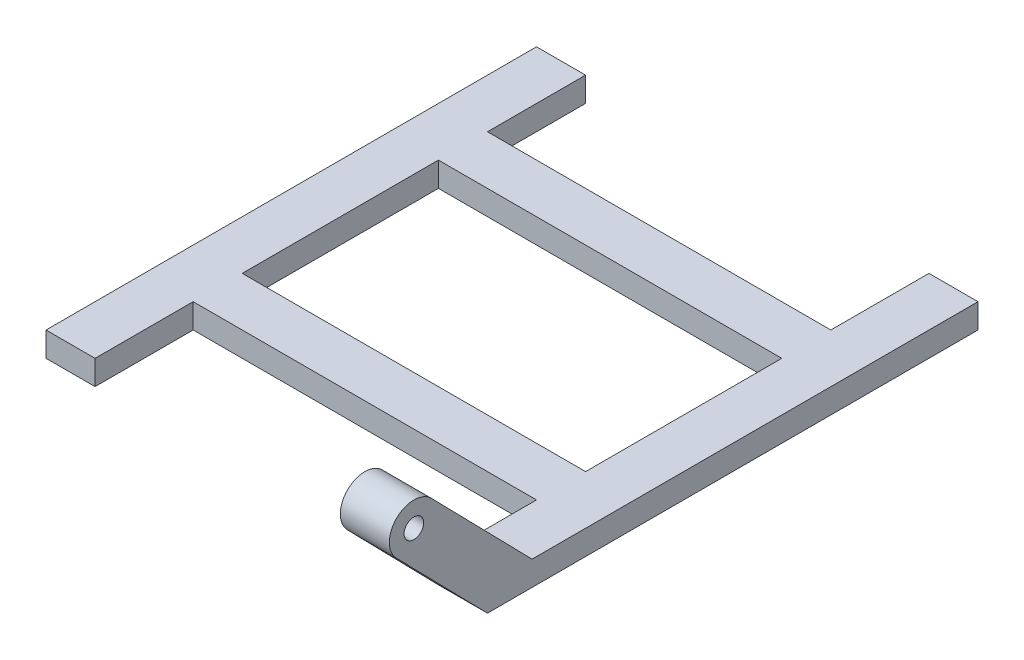
SolidWorks part; units mm, degrees
ref_plane "Plan de face" through (0, 0, 0) normal (0, 0, 1) x (1, 0, 0)
ref_plane "Plan de dessus" through (0, 0, 0) normal (0, 1, 0) x (1, 0, 0)
ref_plane "Plan de droite" through (0, 0, 0) normal (1, 0, 0) x (0, 0, -1)
sketch "Esquisse1" plane through (0, 0, 0) normal (0, 1, 0) x (1, 0, 0)
  line L0 (0, 0) -> (0, -50) construction
  line L1 (-35, -5) -> (35, -5)
  line L2 (-35, -5) -> (-35, 5)
  line L3 (-35, 5) -> (35, 5)
  line L4 (35, -5) -> (35, 5)
  line L5 (-35, -5) -> (35, 5) construction
  line L6 (-35, 5) -> (35, -5) construction
  line L7 (35, 25) -> (45, 25)
  line L8 (35, 25) -> (35, -75)
  line L9 (35, -75) -> (45, -75)
  line L10 (45, 25) -> (45, -75)
  line L11 (-45, 25) -> (-35, 25)
  line L12 (-45, 25) -> (-45, -75)
  line L13 (-45, -75) -> (-35, -75)
  line L14 (-35, 25) -> (-35, -75)
  line L16 (-35, -55) -> (35, -55)
  line L17 (-35, -55) -> (-35, -45)
  line L18 (-35, -45) -> (35, -45)
  line L19 (35, -55) -> (35, -45)
  line L20 (-35, -55) -> (35, -45) construction
  line L21 (-35, -45) -> (35, -55) construction
  point P0 (0, 0)
  point P14 (-40, 25)
  dimension "D1" = 10
  dimension "D2" = 100
  dimension "D3" = 70
  dimension "D4" = 10
  dimension "D5" = 20
  dimension "D6" = 10
  dimension "D7" = 50
extrude "Boss.-Extru.1" add sketch "Esquisse1" along normal blind 5 contours L14 L11 L12 L13 L2 | L1 L4 L3 L2 | L10 L7 L8 L4 L9 | L17 L16 L19 L18
ref_plane "Plan1" through (0, 15, 0) normal (0, 1, 0) x (1, 0, 0)
sketch "Esquisse2" plane through (0, 15, 0) normal (0, 1, 0) x (1, 0, 0)
  line L0 (-40, -90) -> (40, -90) construction
  line L1 (-45, -87) -> (-35, -87)
  line L2 (-45, -87) -> (-45, -93)
  line L3 (-45, -93) -> (-35, -93)
  line L4 (-35, -87) -> (-35, -93)
  line L5 (-45, -87) -> (-35, -93) construction
  line L6 (-45, -93) -> (-35, -87) construction
  line L7 (35, -87) -> (45, -87)
  line L8 (35, -87) -> (35, -93)
  line L9 (35, -93) -> (45, -93)
  line L10 (45, -87) -> (45, -93)
  line L11 (35, -87) -> (45, -93) construction
  line L12 (35, -93) -> (45, -87) construction
  line L13 (0, -90) -> (0, -75) construction
  line L14 (-35, -75) -> (35, -75) construction
  point P0 (-40, -90)
  point P5 (40, -90)
  point P18 (0, -75)
  point P19 (-23.4193, -105.2034)
  point P20 (0, -90)
  point P21 (-45, -94.3736)
  point P22 (-45, -94.8002)
  dimension "D1" = 10
  dimension "D2" = 80
  dimension "D3" = 15
  dimension "D4" = 6
sketch "Esquisse3" plane through (45, 0, 0) normal (1, 0, 0) x (0, 0, -1)
  line L0 (-75, 2.5) -> (-90, 2.5) construction
  line L1 (-75, 5) -> (-75, 0) construction
  line L2 (-90, 2.5) -> (-90, 22.5) construction
  line L3 (-75, 0) -> (-93.5757, 19.0051)
  line L4 (-65.9037, 5) -> (-86.4243, 25.9949)
  line L5 (25, 5) -> (-75, 5) construction
  line L6 (-65.9037, 5) -> (-75, 0)
  circle A0 centre (-90, 22.5) radius 5
  circle A1 centre (-90, 22.5) radius 2
  line M8 (25, 5) -> (-75, 5)
  line M9 (-75, 5) -> (-75, 0)
  dimension "D3" = 10
  dimension "D4" = 4
  dimension "D1" = 20
  dimension "D2" = 15
extrude "Boss.-Extru.2" add sketch "Esquisse3" against normal up to surface (10 mm away) contours A0 L3 L4 M9 M8 | A0 A1 up to face at (35, 2.5, -15)
